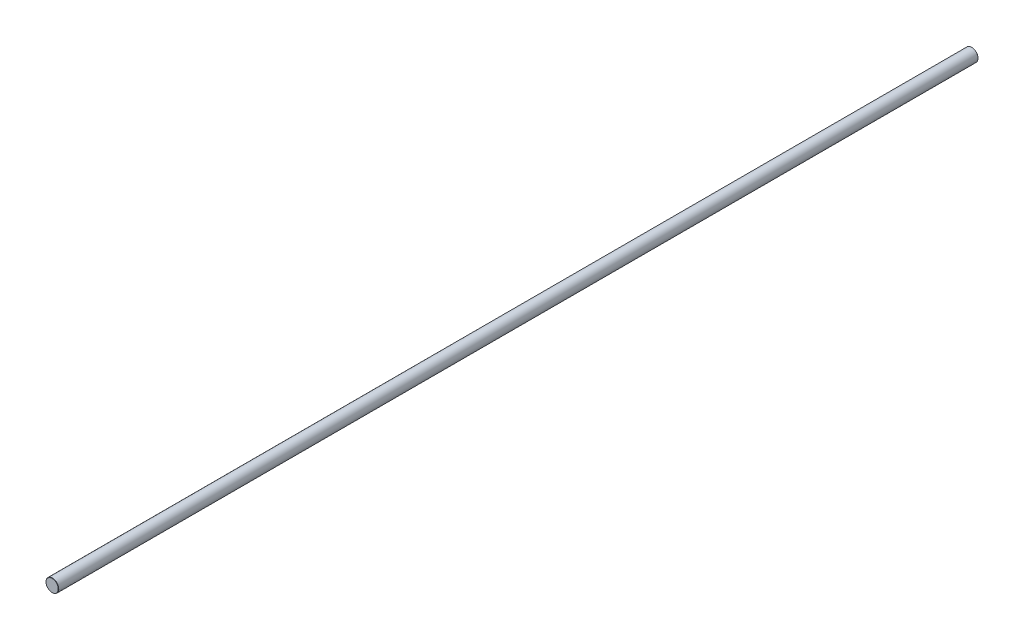
SolidWorks part; units mm, degrees
material "AISI 304"
ref_plane "Front Plane" through (0, 0, 0) normal (0, 0, 1) x (1, 0, 0)
ref_plane "Top Plane" through (0, 0, 0) normal (0, 1, 0) x (1, 0, 0)
ref_plane "Right Plane" through (0, 0, 0) normal (1, 0, 0) x (0, 0, -1)
sketch "Sketch1" plane through (0, 0, 0) normal (0, 0, 1) x (1, 0, 0)
  circle A0 centre (0, 0) radius 6.35 construction
  dimension "Diameter" = 12.7
sketch "Sketch2" plane through (0, 0, 0) normal (1, 0, 0) x (0, 0, -1)
  line L0 (457.2, 0) -> (-457.2, 0) construction
  point P0 (-365.76, 0)
  point P3 (0, 0)
  point P4 (365.76, 0)
  point P6 (-320.04, 0)
  point P7 (320.04, 0)
  dimension "Length" = 914.4
  dimension "D1" = 91.44
  dimension "D2" = 91.44
  dimension "D3" = 137.16
  dimension "D4" = 137.16
sketch "Sketch3" plane through (0, 0, 0) normal (0, 0, 1) x (1, 0, 0)
  circle A0 centre (0, 0) radius 6.35 construction
  circle A1 centre (0, 0) radius 6.35
extrude "Boss-Extrude1" add sketch "Sketch3" along normal up to vertex (457.2 mm away) and the other way up to vertex (457.2 mm away) up to point (0, 0, 457.2) other way up to point (0, 0, -457.2)
chamfer "Chamfer1" distance 0.254 angle 45 2 edges at (6.35, 0, 457.2) (6.35, 0, -457.2)
equation "\"D1@Chamfer1\"=\"Diameter@Sketch1\"*.02"
equation "\"D1@Sketch2\"=\"D2@Sketch2\""
equation "\"D2@Sketch2\"=\"Length@Sketch2\"*.1"
equation "\"D3@Sketch2\"=\"Length@Sketch2\"*.15"
equation "\"D4@Sketch2\"=\"D3@Sketch2\""
